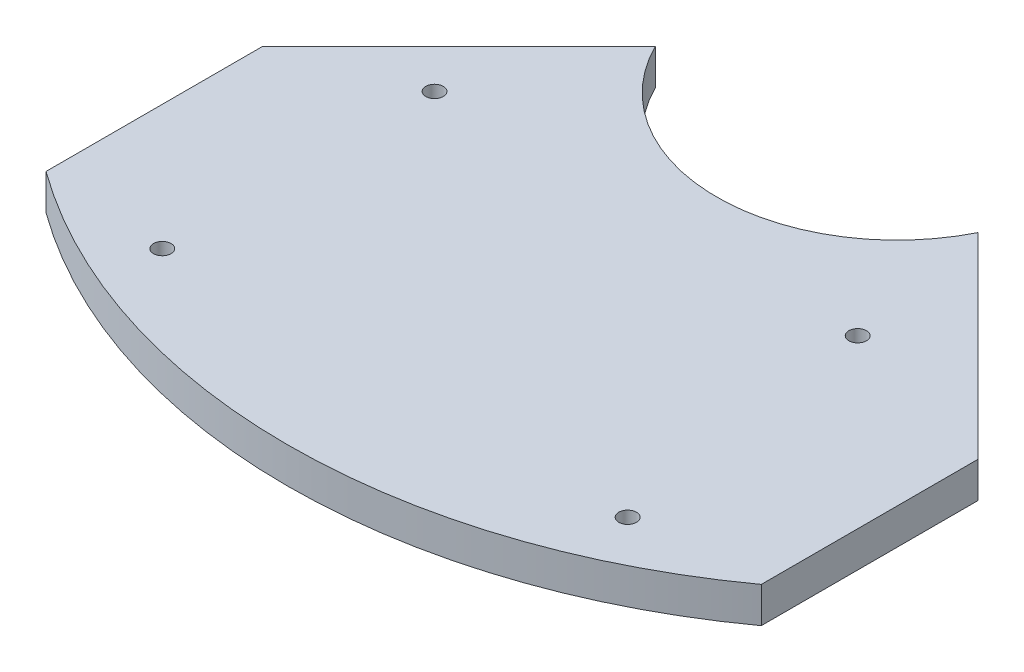
SolidWorks part; units mm, degrees
ref_plane "Front Plane" through (0, 0, 0) normal (0, 0, 1) x (1, 0, 0)
ref_plane "Top Plane" through (0, 0, 0) normal (0, 1, 0) x (1, 0, 0)
ref_plane "Right Plane" through (0, 0, 0) normal (1, 0, 0) x (0, 0, -1)
sketch "Sketch1" plane through (0, 0, 0) normal (0, 1, 0) x (1, 0, 0)
  line L0 (35.179, 108.204) -> (-35.179, 108.204) construction
  line L2 (-63.5, 59.0724) -> (-63.5, 20.592)
  line L5 (0, 0) -> (0, 76.2)
  line L6 (-14.3684, 108.204) -> (-57.2306, 65.3418) construction
  line L8 (0, -33.935) -> (0, 81.7042) construction
  line L9 (0, 108.204) -> (-35.3405, 72.8635) construction
  line L10 (-28.6438, 93.9286) -> (-63.5, 59.0724)
  arc A0 (-28.6438, 93.9286) -> (0, 76.2) centre (0, 108.204) ccw
  arc A1 (-63.5, 20.592) -> (0, 0) centre (0, 108.204) ccw
  dimension "D3" = 64.008
  dimension "D1" = 63.5
  dimension "D2" = 76.2
  dimension "D4" = 45
  dimension "D5" = 10.16
extrude "Boss-Extrude1" add sketch "Sketch1" along normal blind 6.35
ref_plane "Plane1" through (0, 0, 0) normal (1, 0, 0) x (0, 0, -1)
mirror "Mirror1" about plane through (0, 0, 0) normal (1, 0, 0) of "Boss-Extrude1"
sketch "Sketch3" plane through (0, 6.35, 0) normal (0, 1, 0) x (1, 0, 0)
  line L0 (0, -7.1183) -> (0, 45.2183) construction
  line L1 (-41.3131, 19.05) -> (41.3131, 19.05) construction
  line L4 (-41.3131, 67.3862) -> (33.8201, 67.3862) construction
  circle A0 centre (-41.3131, 19.05) radius 1.5621
  circle A1 centre (41.3131, 19.05) radius 1.5621
  circle A2 centre (-41.3131, 67.3862) radius 1.5621
  circle A3 centre (33.8201, 67.3862) radius 1.5621
  point P5 (0, 19.05)
  dimension "D5" = 3.1242
  dimension "D6" = 3.1242
  dimension "D7" = 3.1242
  dimension "D1" = 82.6262
  dimension "D2" = 19.05
  dimension "D3" = 75.1332
  dimension "D4" = 48.3362
extrude "Cut-Extrude1" cut sketch "Sketch3" against normal through all
